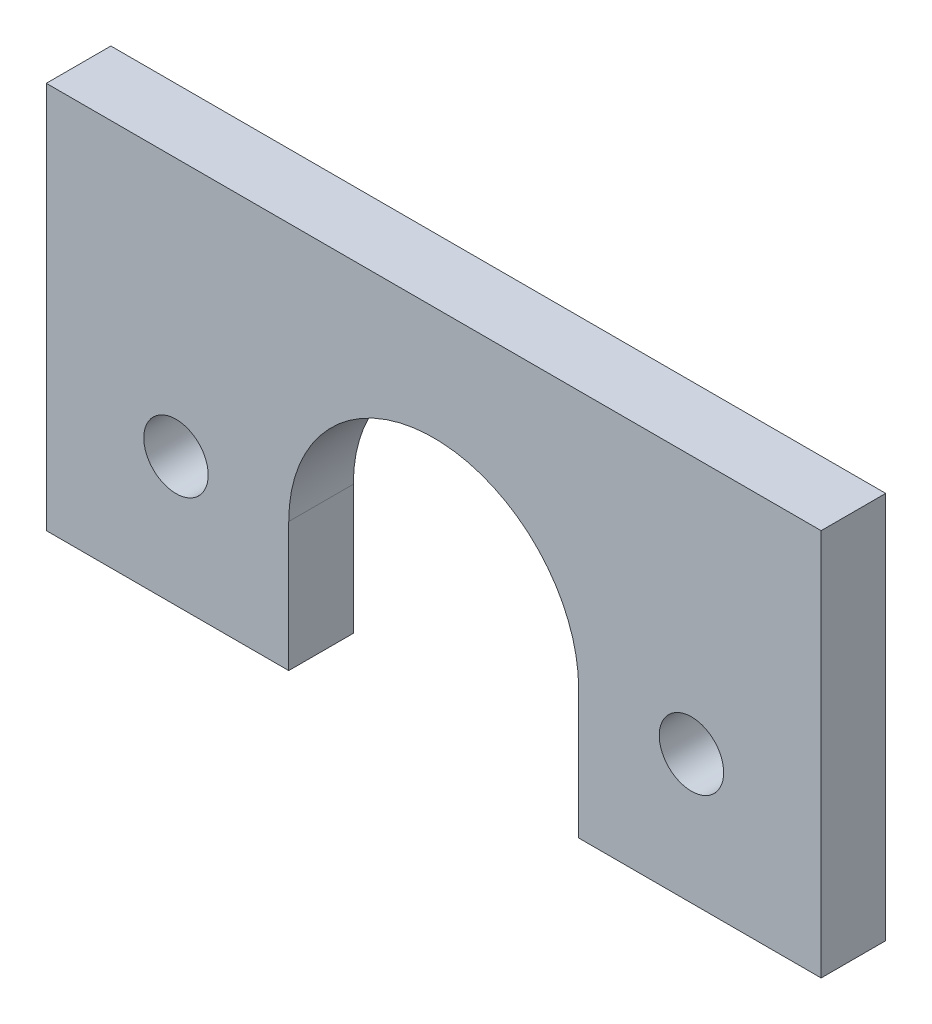
SolidWorks part; units mm, degrees
ref_plane "Front Plane" through (0, 0, 0) normal (0, 0, 1) x (1, 0, 0)
ref_plane "Top Plane" through (0, 0, 0) normal (0, 1, 0) x (1, 0, 0)
ref_plane "Right Plane" through (0, 0, 0) normal (1, 0, 0) x (0, 0, -1)
sketch "Sketch1" plane through (0, 0, 0) normal (0, 0, 1) x (1, 0, 0)
  line L0 (0, -25.0958) -> (0, 0.2498) construction
  line L1 (-14.2569, 0.2498) -> (-14.2569, 12.9226) construction
  line L2 (14.2569, 0.2498) -> (14.2569, 12.9226) construction
  line L3 (14.2569, 12.9226) -> (14.2569, 25.0958) construction
  line L4 (14.2569, 25.0958) -> (-14.2569, 25.0958) construction
  line L5 (-14.2569, 25.0958) -> (-14.2569, 12.9226) construction
  line L6 (0, 0.2498) -> (-25.3456, 0.2498) construction
  line L7 (-25.3456, 0.2498) -> (-25.3456, 12.9226) construction
  line L8 (-14.2569, 0.2498) -> (-14.2569, -12.4502)
  line L9 (-14.2569, -12.4502) -> (-38.1, -12.4502)
  line L10 (-38.1, -12.4502) -> (-38.1, 25.6498)
  line L11 (-38.1, 25.6498) -> (38.1, 25.6498)
  line L12 (0, 25.6498) -> (0, 0.2498) construction
  line L13 (14.2569, 0.2498) -> (14.2569, -12.4502)
  line L14 (14.2569, -12.4502) -> (38.1, -12.4502)
  line L15 (38.1, -12.4502) -> (38.1, 25.6498)
  circle A0 centre (0, 0.2498) radius 14.2569 construction
  circle A1 centre (-25.3456, 0.2498) radius 3.1682 construction
  circle A2 centre (25.3456, 0.2498) radius 3.1682 construction
  arc A3 (-14.2569, 0.2498) -> (14.2569, 0.2498) centre (0, 0.2498) cw
  circle A4 centre (-25.3456, 0.2498) radius 3.1682
  circle A5 centre (25.3456, 0.2498) radius 3.1682
  dimension "D1" = 38.1
  dimension "D2" = 38.1
  dimension "D3" = 25.4
extrude "Boss-Extrude1" add sketch "Sketch1" along normal blind 6.35 contours L8 A3 L13 L14 L15 L11 L10 L9 A4 A5
